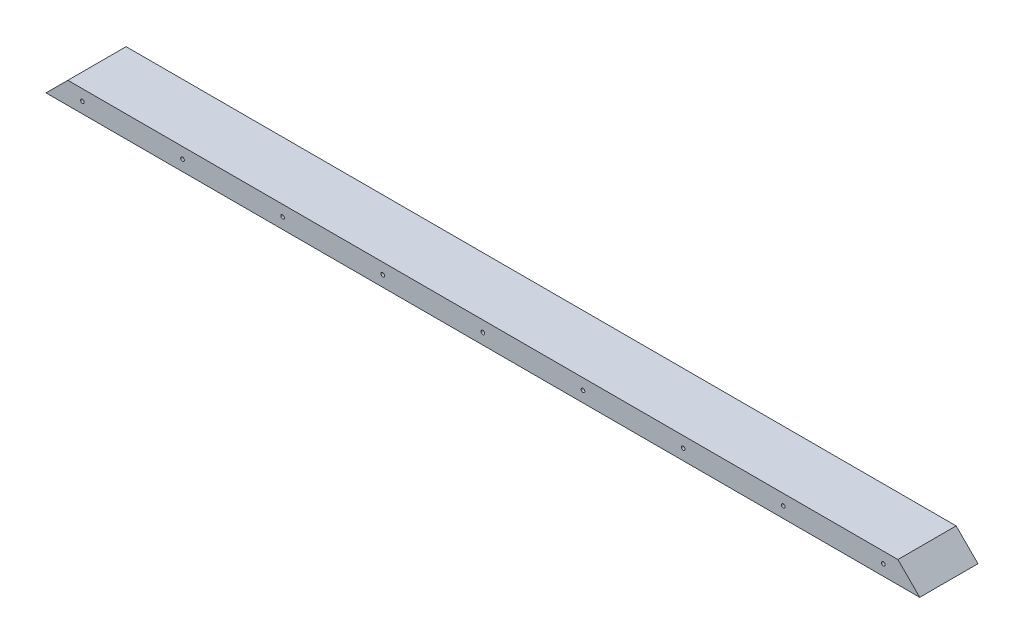
SolidWorks part; units mm, degrees
ref_plane "Alzado" through (0, 0, 0) normal (0, 0, 1) x (1, 0, 0)
ref_plane "Planta" through (0, 0, 0) normal (0, 1, 0) x (1, 0, 0)
ref_plane "Vista lateral" through (0, 0, 0) normal (1, 0, 0) x (0, 0, -1)
sketch "Croquis1" plane through (0, 0, 0) normal (1, 0, 0) x (0, 0, -1)
  line L0 (-20, 0) -> (20, 0)
  line L1 (20, 0) -> (20, 15)
  line L2 (20, 15) -> (18.5, 15)
  line L6 (-18.5, 15) -> (-20, 15)
  line L7 (-20, 15) -> (-20, 0)
  line L8 (-18.5, 15) -> (18.5, 15)
  point P4 (0, 0)
extrude "Saliente-Extruir1" add sketch "Croquis1" along normal blind 600
sketch "Croquis2" plane through (0, 0, -20) normal (0, 0, -1) x (-1, 0, 0)
  line L0 (-600, 15) -> (-585, 15)
  line L1 (-585, 15) -> (-600, 0)
  line L2 (-600, 0) -> (-600, 15)
  line L3 (0, 15) -> (-15, 15)
  line L4 (-600, 15) -> (0, 15) construction
  line L5 (-15, 15) -> (0, 0)
  line L6 (0, 0) -> (0, 15)
  line L7 (0, 0) -> (-600, 0) construction
  line L8 (-7.5, 7.5) -> (-592.5, 7.5) construction
  line L9 (-7.5, 7.5) -> (-25, 7.5) construction
  line L10 (-25, 7.5) -> (-300, 7.5) construction
  line L11 (-300, 7.5) -> (-162.5, 7.5) construction
  line L12 (-162.5, 7.5) -> (-25, 7.5) construction
  line L13 (-25, 7.5) -> (-93.75, 7.5) construction
  line L14 (-93.75, 7.5) -> (-300, 7.5) construction
  line L15 (-300, 7.5) -> (-162.5, 7.5) construction
  line L16 (-162.5, 7.5) -> (-231.25, 7.5) construction
  line L17 (-437.5, 7.5) -> (-368.75, 7.5) construction
  line L18 (-575, 7.5) -> (-506.25, 7.5) construction
  line L19 (-437.5, 7.5) -> (-575, 7.5) construction
  circle A0 centre (-25, 7.5) radius 1.25
  circle A1 centre (-93.75, 7.5) radius 1.25
  circle A2 centre (-162.5, 7.5) radius 1.25
  circle A3 centre (-231.25, 7.5) radius 1.25
  circle A4 centre (-368.75, 7.5) radius 1.25
  circle A5 centre (-437.5, 7.5) radius 1.25
  circle A6 centre (-506.25, 7.5) radius 1.25
  circle A7 centre (-575, 7.5) radius 1.25
  circle A8 centre (-300, 7.5) radius 1.25
extrude "Cortar-Extruir1" cut sketch "Croquis2" against normal through all
